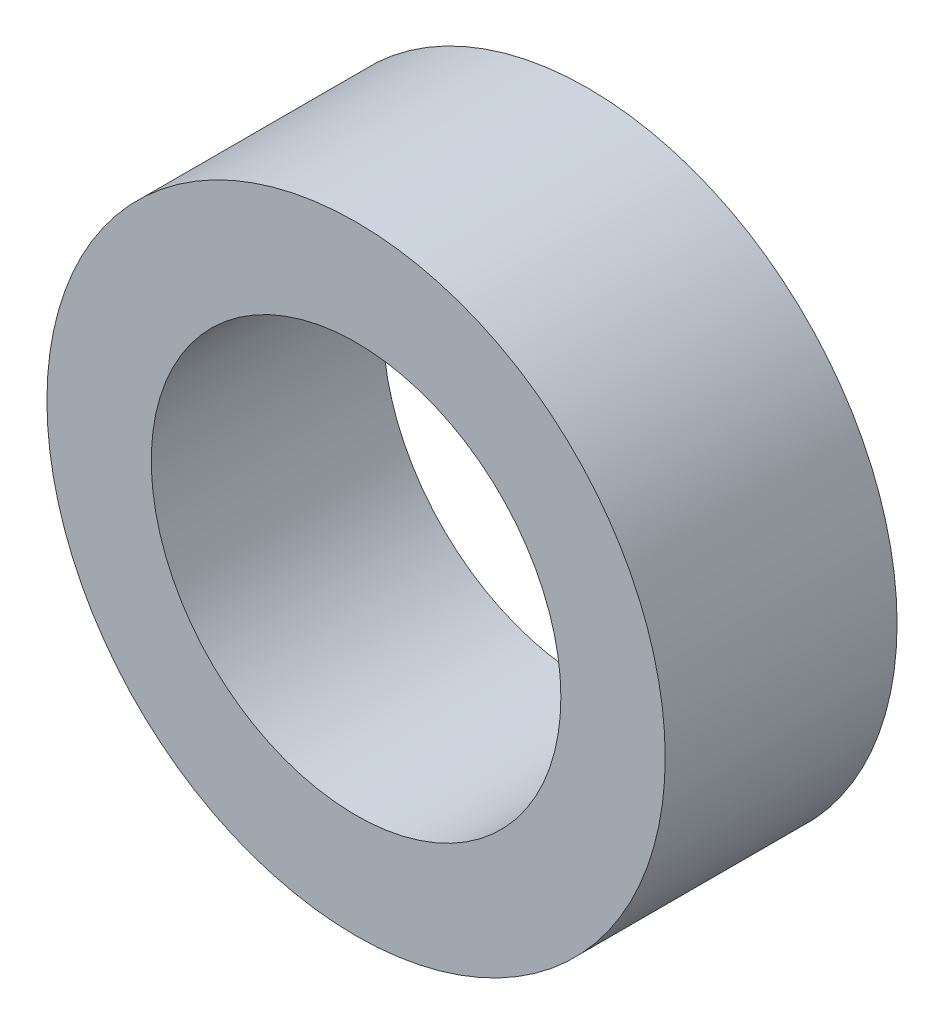
SolidWorks part; units mm, degrees
ref_plane "Front Plane" through (0, 0, 0) normal (0, 0, 1) x (1, 0, 0)
ref_plane "Top Plane" through (0, 0, 0) normal (0, 1, 0) x (1, 0, 0)
ref_plane "Right Plane" through (0, 0, 0) normal (1, 0, 0) x (0, 0, -1)
sketch "Sketch1" plane through (0, 0, 0) normal (0, 0, 1) x (1, 0, 0)
  circle A0 centre (0, 0) radius 4
  circle A1 centre (0, 0) radius 2.65
  dimension "OD" = 8
  dimension "ID" = 5.3
extrude "Extrude1" add sketch "Sketch1" along normal mid plane 3
sketch "Sketch2" plane through (0, 0, 0) normal (1, 0, 0) x (0, 0, -1)
  line L0 (-1.5, -2.65) -> (1.5, -2.65) construction
  line L3 (1.5, 2.65) -> (-1.5, 2.65) construction
  line L5 (-1.5, -2.65) -> (1.5, -2.65)
  line L6 (1.5, 2.65) -> (-1.5, 2.65)
sketch "Sketch4" plane through (0, 0, 1.5) normal (0, 0, 1) x (1, 0, 0)
  line L0 (0, 0) -> (-1.8738, 1.8738)
  line L1 (0, -1.1) -> (0, 1.1) construction
  circle A0 centre (0, 0) radius 2.65 construction
  dimension "D1" = 45
